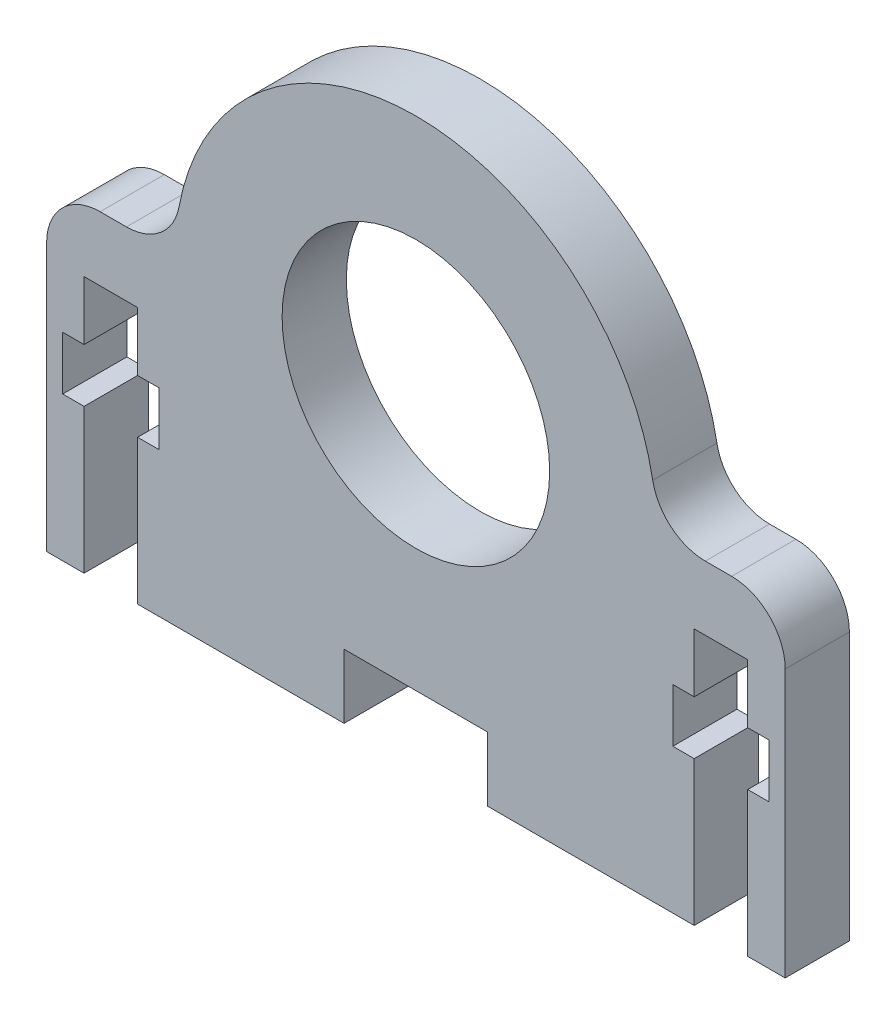
SolidWorks part; units mm, degrees
material "Pine"
ref_plane "Front Plane" through (0, 0, 0) normal (0, 0, 1) x (1, 0, 0)
ref_plane "Top Plane" through (0, 0, 0) normal (0, 1, 0) x (1, 0, 0)
ref_plane "Right Plane" through (0, 0, 0) normal (1, 0, 0) x (0, 0, -1)
sketch "Sketch1" plane through (0, 0, 0) normal (0, 0, 1) x (1, 0, 0)
  line L0 (-22.5, 0) -> (-22.5, -30)
  line L1 (-22.5, -30) -> (-6.7072, -30)
  line L2 (-6.7072, -30) -> (-6.7072, -24)
  line L3 (-6.7072, -24) -> (6.7072, -24)
  line L4 (6.7072, -24) -> (6.7072, -30)
  line L5 (6.7072, -30) -> (22.5, -30)
  line L6 (22.5, 0) -> (22.5, -30)
  circle A0 centre (0, 0) radius 12.5
  arc A1 (22.5, 0) -> (-22.5, 0) centre (0, 0) ccw
  dimension "D1" = 25
  dimension "D2" = 45
  dimension "D3" = 30
  dimension "D4" = 15.7928
  dimension "D5" = 6
extrude "Boss-Extrude1" add sketch "Sketch1" along normal blind 6
sketch "Sketch2" plane through (0, 0, 0) normal (0, 0, 1) x (1, 0, 0)
  line L0 (-28.5, -30) -> (-28.5, 2) construction
  line L1 (-22.5, -30) -> (-26, -30)
  line L2 (-22.5, -30) -> (-22.5, 0)
  line L3 (-22.5, 0) -> (-34.5, 0)
  line L4 (-34.5, -30) -> (-34.5, 0)
  line L5 (-26, -30) -> (-26, -16.5)
  line L6 (-31, -30) -> (-31, -16.5)
  line L7 (-31, -6) -> (-26, -6)
  line L8 (-33, -11.5) -> (-31, -11.5)
  line L9 (-33, -11.5) -> (-33, -16.5)
  line L10 (-33, -16.5) -> (-31, -16.5)
  line L11 (-24, -11.5) -> (-24, -16.5)
  line L12 (-33, -11.5) -> (-24, -16.5) construction
  line L13 (-33, -16.5) -> (-24, -11.5) construction
  line L14 (-34.5, -30) -> (-31, -30)
  line L16 (-26, -11.5) -> (-26, -6)
  line L17 (-31, -11.5) -> (-31, -6)
  line L18 (-26, -16.5) -> (-24, -16.5)
  line L19 (-26, -11.5) -> (-24, -11.5)
  point P13 (-28.5, -14)
  dimension "D1" = 12
  dimension "D2" = 30
  dimension "D3" = 5
  dimension "D4" = 2.5
  dimension "D5" = 5
  dimension "D6" = 16
  dimension "D7" = 9
  dimension "D8" = 24
extrude "Boss-Extrude2" add sketch "Sketch2" along normal blind 6
mirror "Mirror1" about plane through (0, 0, 0) normal (1, 0, 0) of "Boss-Extrude2"
fillet "Fillet1" radius 5 4 edges at (-34.5, 0, 3) (34.5, 0, 3) (22.5, 0, 3) (-22.5, 0, 3)
